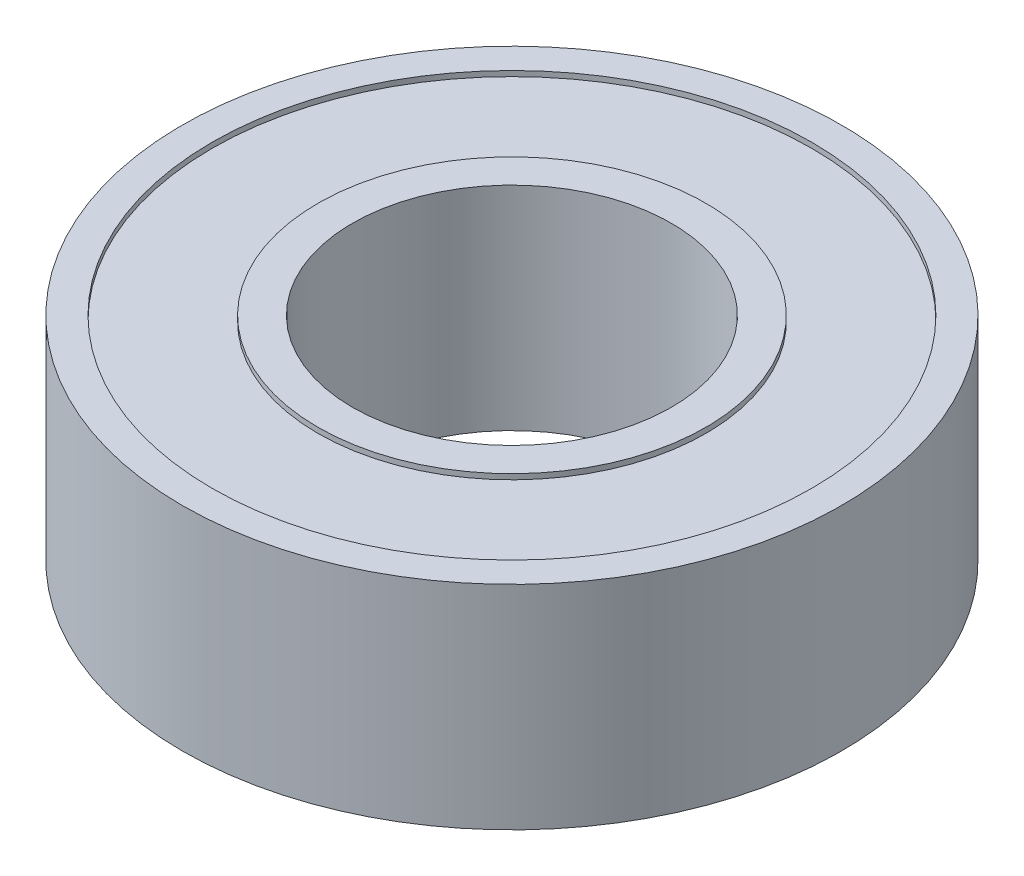
SolidWorks part; units mm, degrees
ref_plane "Front Plane" through (0, 0, 0) normal (0, 0, 1) x (1, 0, 0)
ref_plane "Top Plane" through (0, 0, 0) normal (0, 1, 0) x (1, 0, 0)
ref_plane "Right Plane" through (0, 0, 0) normal (1, 0, 0) x (0, 0, -1)
sketch "Sketch1" plane through (0, 0, 0) normal (0, 1, 0) x (1, 0, 0)
  circle A0 centre (0, 0) radius 15
  circle A1 centre (0, 0) radius 31
  dimension "D1" = 62
  dimension "D2" = 30
extrude "Boss-Extrude1" add sketch "Sketch1" along normal blind 20
sketch "Sketch2" plane through (0, 20, 0) normal (0, 1, 0) x (1, 0, 0)
  circle A0 centre (0, 0) radius 28.2
  circle A1 centre (0, 0) radius 18.25
  dimension "D1" = 56.4
  dimension "D2" = 36.5
extrude "Cut-Extrude1" cut sketch "Sketch2" against normal blind 0.5
sketch "Sketch3" plane through (0, 0, 0) normal (0, -1, 0) x (1, 0, 0)
  circle A0 centre (0, 0) radius 18.25 construction
  circle A1 centre (0, 0) radius 28.2
  circle A2 centre (0, 0) radius 28.2
  circle A3 centre (0, 0) radius 18.25
  dimension "D1" = 0
extrude "Cut-Extrude2" cut sketch "Sketch3" against normal blind 0.5
